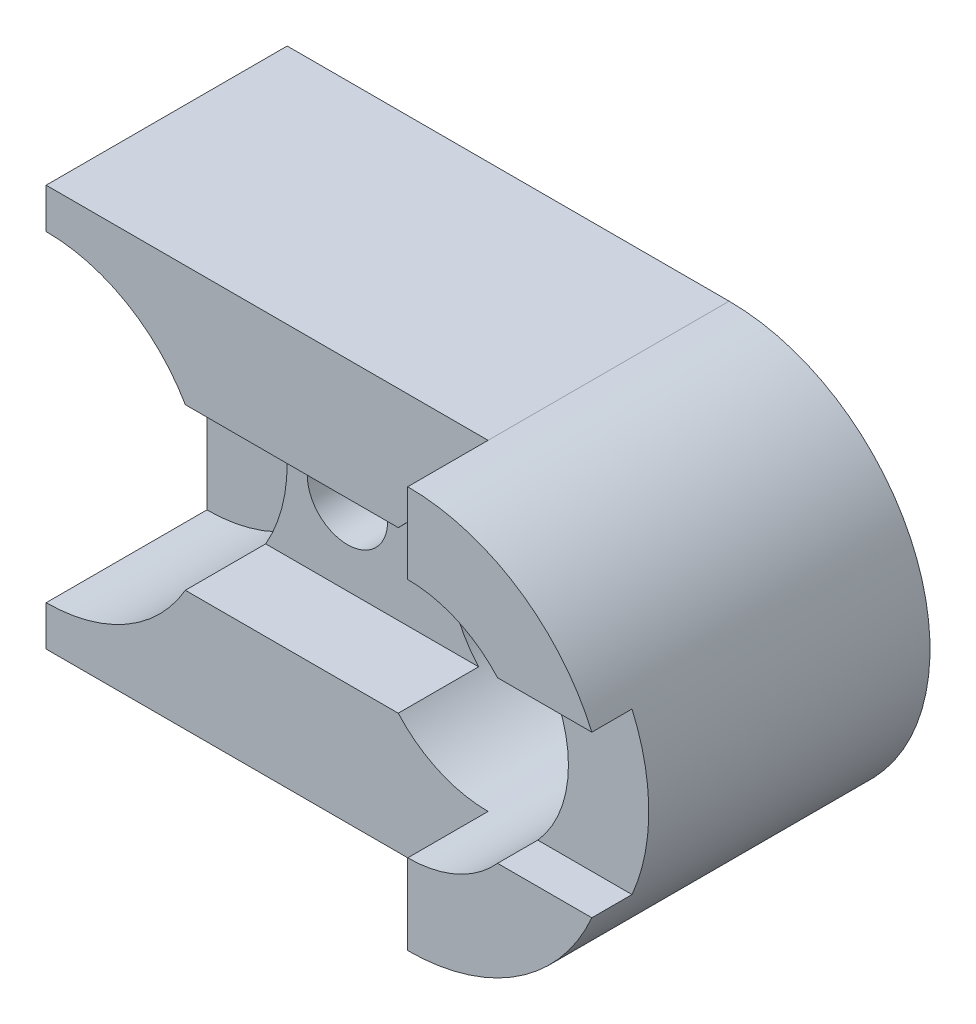
SolidWorks part; units mm, degrees
ref_plane "Front" through (0, 0, 0) normal (0, 0, 1) x (1, 0, 0)
ref_plane "Top" through (0, 0, 0) normal (0, 1, 0) x (1, 0, 0)
ref_plane "Right" through (0, 0, 0) normal (1, 0, 0) x (0, 0, -1)
sketch "Sketch1" plane through (0, 0, 0) normal (0, 0, 1) x (1, 0, 0)
  line L1 (-5.5, -5) -> (5.5, -5)
  line L2 (-5.5, -5) -> (-5.5, 5)
  line L3 (-5.5, 5) -> (5.5, 5)
  line L5 (-5.5, -5) -> (5.5, 5) construction
  line L6 (-5.5, 5) -> (5.5, -5) construction
  arc A0 (5.5, 5) -> (5.5, -5) centre (5.5, 0) cw
  circle A1 centre (5.5, 0) radius 1.25
  circle A2 centre (-5.5, 0) radius 2
  circle A3 centre (0, 0) radius 1
  point P0 (0, 0)
  dimension "D3" = 2.5
  dimension "D4" = 2
  dimension "D5" = 4
  dimension "D1" = 10
  dimension "D2" = 11
extrude "Boss-Extrude1" add sketch "Sketch1" along normal blind 8 contours A2 L2 L1 A0 L3 A3 A1
sketch "Sketch2" plane through (-5.5, 0, 0) normal (-1, 0, 0) x (0, 0, 1)
  line L0 (8, -2) -> (0, -2) construction
  line L1 (8, 2) -> (7, 2)
  line L2 (8, 2) -> (8, -2)
  line L3 (8, -2) -> (7, -2)
  line L4 (7, 2) -> (7, -2)
  dimension "D1" = 1
extrude "Cut-Extrude1" cut sketch "Sketch2" against normal blind 18
sketch "Sketch3" plane through (0, 0, 8) normal (0, 0, 1) x (1, 0, 0)
  line L0 (5.5, 5) -> (5.5, 3)
  line L1 (5.5, -3) -> (5.5, -5)
  line L2 (5.5, 5) -> (5.5, 6.3247)
  line L3 (5.5, 6.3247) -> (-9.4346, 6.1086)
  line L4 (-9.4346, 6.1086) -> (-8.5869, -6.4576)
  line L5 (-8.5869, -6.4576) -> (-0.1263, -6.6737)
  line L6 (-0.1263, -6.6737) -> (5.5, -5)
  arc A0 (5.5, 5) -> (5.5, -5) centre (5.5, 0) cw
  arc A1 (5.5, -3) -> (5.5, 3) centre (5.5, 0) ccw
  line M5 (10.0826, -2) -> (-5.5, -2)
  line M6 (-5.5, -2) -> (-5.5, -5)
  line M7 (-5.5, -5) -> (5.5, -5)
  dimension "D1" = 6
extrude "Cut-Extrude2" cut sketch "Sketch3" against normal blind 2 contours A1 L0 L2 L3 L4 L5 L6 M5 M7 M6 | L1 A1 M5 M6 M7
sketch "Sketch4" plane through (-5.5, 0, 0) normal (-1, 0, 0) x (0, 0, 1)
  line L0 (6, -2) -> (0, -2) construction
  line L1 (6, 2) -> (4, 2)
  line L2 (6, 2) -> (6, -2)
  line L3 (6, -2) -> (4, -2)
  line L4 (4, 2) -> (4, -2)
  dimension "D1" = 2
extrude "Cut-Extrude3" cut sketch "Sketch4" against normal blind 11
sketch "Sketch5" plane through (0, 0, 6) normal (0, 0, 1) x (1, 0, 0)
  circle A0 centre (5.5, 0) radius 3
  dimension "D1" = 6
extrude "Cut-Extrude4" cut sketch "Sketch5" against normal blind 3
sketch "Sketch6" plane through (0, 0, 6) normal (0, 0, 1) x (1, 0, 0)
  circle A0 centre (-5.5, 0) radius 4
  dimension "D1" = 8
extrude "Cut-Extrude5" cut sketch "Sketch6" against normal blind 4
